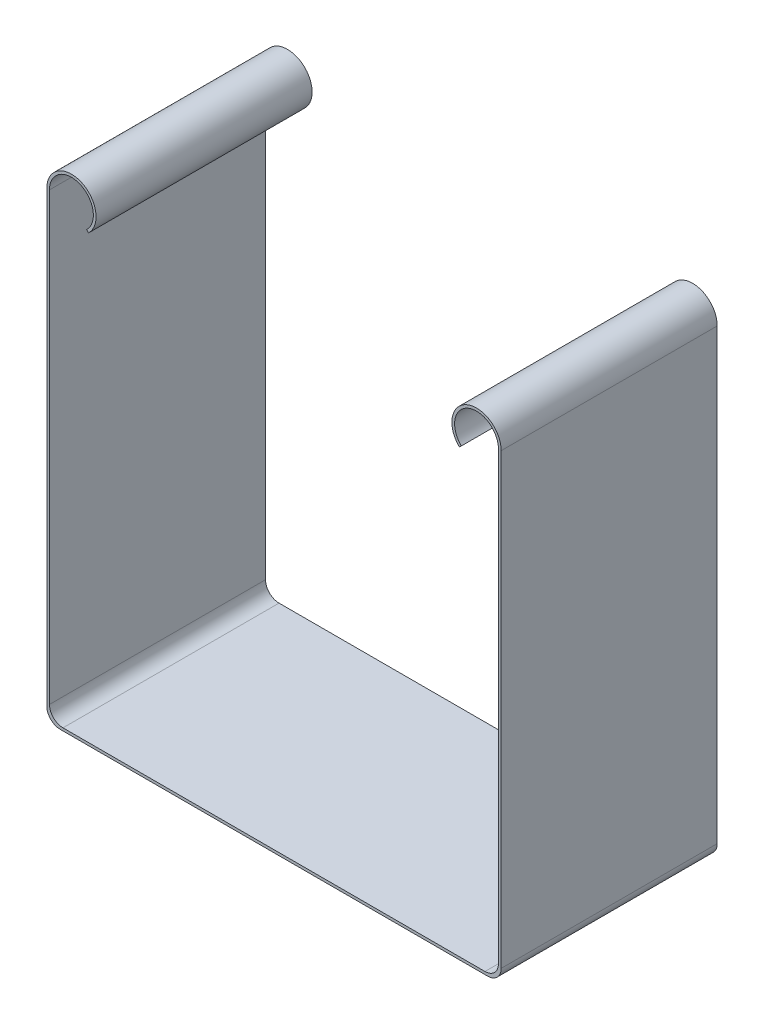
SolidWorks part; units mm, degrees
ref_plane "Plan de face" through (0, 0, 0) normal (0, 0, 1) x (1, 0, 0)
ref_plane "Plan de dessus" through (0, 0, 0) normal (0, 1, 0) x (1, 0, 0)
ref_plane "Plan de droite" through (0, 0, 0) normal (1, 0, 0) x (0, 0, -1)
sketch "Esquisse1" plane through (0, 0, 0) normal (0, 0, 1) x (1, 0, 0)
  line L13 (0, -0.15) -> (0, 72.4519) construction
  line L14 (33.25, 68) -> (33.25, 34)
  line L15 (33.25, 34) -> (33.25, 0)
  line L16 (33.25, 0) -> (0, 0)
  line L17 (33.65, 68) -> (33.65, 34)
  line L18 (33.65, 34) -> (33.65, -0.4)
  line L19 (33.65, -0.4) -> (0, -0.4)
  line L20 (0, -0.4) -> (0, 0)
  line L21 (27.75, 65.6548) -> (27.4671, 65.3719)
  line L22 (33.65, 68) -> (33.65, 34) construction
  arc A0 (33.25, 68) -> (27.75, 65.6548) centre (30, 68) ccw
  circle A3 centre (30, 34) radius 3.25 construction
  arc A7 (33.65, 68) -> (27.4671, 65.3719) centre (30, 68) ccw
  point P9 (27.2313, 65.1361)
  point P13 (30.06, 67.3458)
  point P16 (27.578, 65.4828)
  point P18 (26.75, 68)
  point P19 (0, 0)
  dimension "D14" = 6.5
  dimension "D5" = 3.65
  dimension "D2" = 34
  dimension "D3" = 33.25
  dimension "D4" = 0.4
  dimension "D6" = 45
  dimension "D7" = 1
  dimension "D11" = 34
extrude "Boss.-Extru.2" add sketch "Esquisse1" along normal blind 32
fillet "Congé2" radius 2 2 edges at (33.25, 0, 16) (33.65, -0.4, 16)
mirror "Symétrie2" about plane through (0, -0.4, 32) normal (1, 0, 0) of bodies 110
